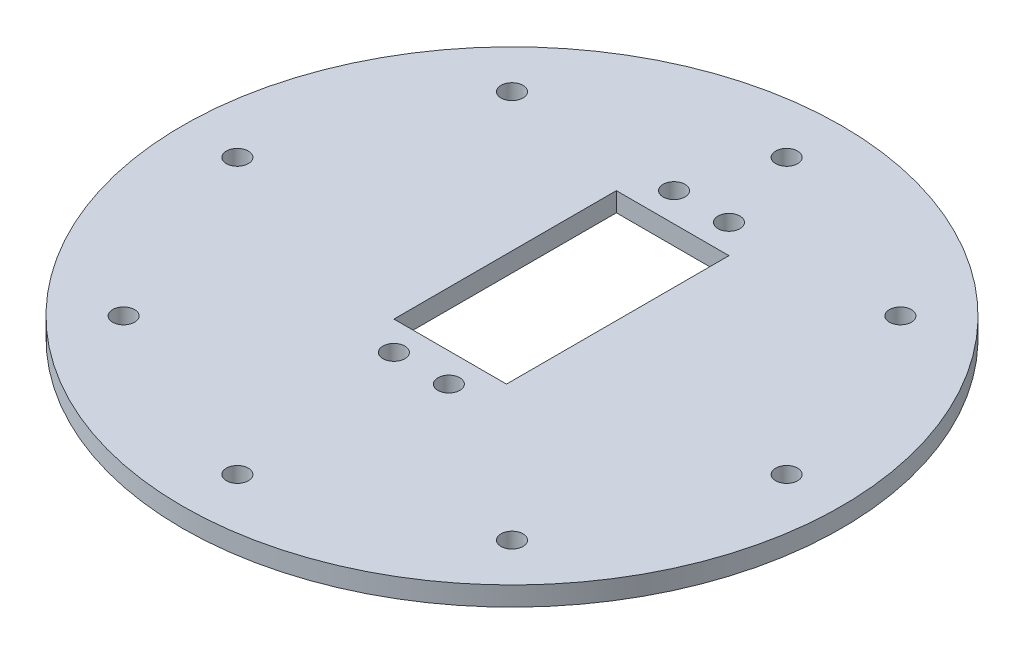
SolidWorks part; units mm, degrees
material "Balsa"
ref_plane "Alzado" through (0, 0, 0) normal (0, 0, 1) x (1, 0, 0)
ref_plane "Planta" through (0, 0, 0) normal (0, 1, 0) x (1, 0, 0)
ref_plane "Vista lateral" through (0, 0, 0) normal (1, 0, 0) x (0, 0, -1)
sketch "Croquis1" plane through (0, 0, 0) normal (0, 1, 0) x (1, 0, 0)
  circle A0 centre (0, 0) radius 60
  circle A1 centre (0, 42) radius 1.8585
  dimension "D1" = 42
extrude "Saliente-Extruir1" add sketch "Croquis1" along normal blind 3.5 contours A0
sketch "Croquis2" plane through (0, 3.5, 0) normal (0, 1, 0) x (1, 0, 0)
  circle A0 centre (0, 50) radius 2
  dimension "D1" = 50
extrude "Cortar-Extruir1" cut sketch "Croquis2" against normal up to next (3.5 mm away)
pattern_circular "MatrizC1" count 8 every 45 about axis through (0, 0, 0) along (0, 1, 0) of "Cortar-Extruir1"
sketch "Croquis3" plane through (0, 3.5, 0) normal (0, 1, 0) x (1, 0, 0)
  line L5 (10.25, 29.25) -> (-10.25, 29.25)
  line L6 (10.25, 29.25) -> (10.25, -11.25)
  line L7 (10.25, -11.25) -> (-10.25, -11.25)
  line L8 (-10.25, 29.25) -> (-10.25, -11.25)
  line L9 (10.25, 29.25) -> (-10.25, -11.25) construction
  line L10 (10.25, -11.25) -> (-10.25, 29.25) construction
  point P0 (0, 9)
  point P1 (0, 9)
  dimension "D1" = 9
  dimension "D2" = 20.5
  dimension "D3" = 40.5
extrude "Cortar-Extruir2" cut sketch "Croquis3" against normal up to next
sketch "Croquis5" plane through (0, 3.5, 0) normal (0, 1, 0) x (1, 0, 0)
  line L0 (0, 9) -> (0, 14.0927) construction
  line L1 (0, 14.0927) -> (0, 3.9679) construction
  line L2 (0, 3.9679) -> (0, 9) construction
  line L3 (0, 9) -> (-5.1993, 9) construction
  line L4 (-5.1993, 9) -> (5, 9) construction
  circle A0 centre (5, 34.5) radius 2
  circle A1 centre (-5, 34.5) radius 2
  circle A2 centre (-5, -16.5) radius 2
  circle A3 centre (5, -16.5) radius 2
  point P2 (0, 9)
  dimension "D1" = 9
  dimension "D2" = 25.5
  dimension "D3" = 5
extrude "Cortar-Extruir4" cut sketch "Croquis5" against normal up to next
